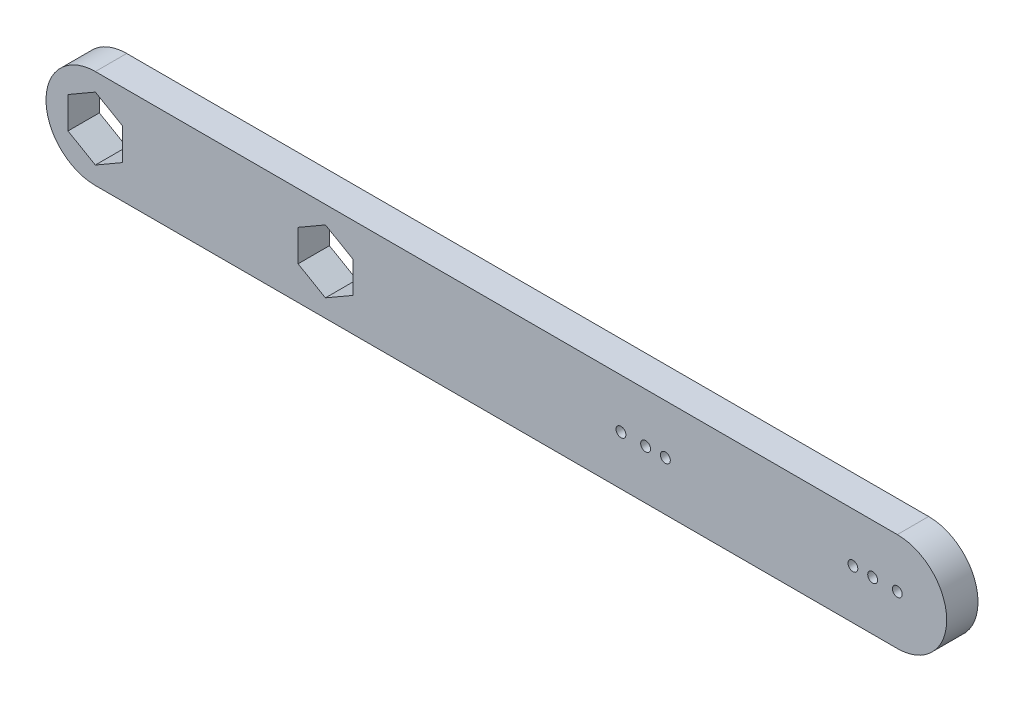
SolidWorks part; units mm, degrees
ref_plane "Front Plane" through (0, 0, 0) normal (0, 0, 1) x (1, 0, 0)
ref_plane "Top Plane" through (0, 0, 0) normal (0, 1, 0) x (1, 0, 0)
ref_plane "Right Plane" through (0, 0, 0) normal (1, 0, 0) x (0, 0, -1)
sketch "Sketch1" plane through (0, 0, 0) normal (0, 0, 1) x (1, 0, 0)
  line L0 (0, 5) -> (81.25, 5)
  line L1 (0, -5) -> (81.25, -5)
  line L3 (0, 3.2) -> (-2.7713, 1.6)
  line L4 (-2.7713, 1.6) -> (-2.7713, -1.6)
  line L5 (-2.7713, -1.6) -> (0, -3.2)
  line L6 (0, -3.2) -> (2.7713, -1.6)
  line L7 (2.7713, -1.6) -> (2.7713, 1.6)
  line L8 (2.7713, 1.6) -> (0, 3.2)
  line L9 (26.0813, 1.6) -> (23.31, 3.2)
  line L10 (23.31, 3.2) -> (20.5387, 1.6)
  line L11 (20.5387, 1.6) -> (20.5387, -1.6)
  line L12 (20.5387, -1.6) -> (23.31, -3.2)
  line L13 (23.31, -3.2) -> (26.0813, -1.6)
  line L14 (26.0813, -1.6) -> (26.0813, 1.6)
  arc A0 (0, 5) -> (0, -5) centre (0, 0) ccw
  arc A1 (81.25, -5) -> (81.25, 5) centre (81.25, 0) ccw
  circle A2 centre (0, 0) radius 2.7713 construction
  circle A3 centre (23.31, 0) radius 2.7713 construction
  circle A4 centre (81.25, 0) radius 0.5
  circle A5 centre (53.25, 0) radius 0.5
  circle A6 centre (55.75, 0) radius 0.5
  circle A7 centre (57.75, 0) radius 0.5
  circle A8 centre (78.75, 0) radius 0.5
  circle A9 centre (76.75, 0) radius 0.5
  dimension "D1" = 5
  dimension "D6" = 1
  dimension "D7" = 2.5
  dimension "D2" = 81.25
  dimension "D3" = 23.31
  dimension "D4" = 3.2
  dimension "D5" = 28
  dimension "D8" = 2
  dimension "D9" = 2
  dimension "D10" = 2.5
extrude "Boss-Extrude1" add sketch "Sketch1" along normal blind 3.175
